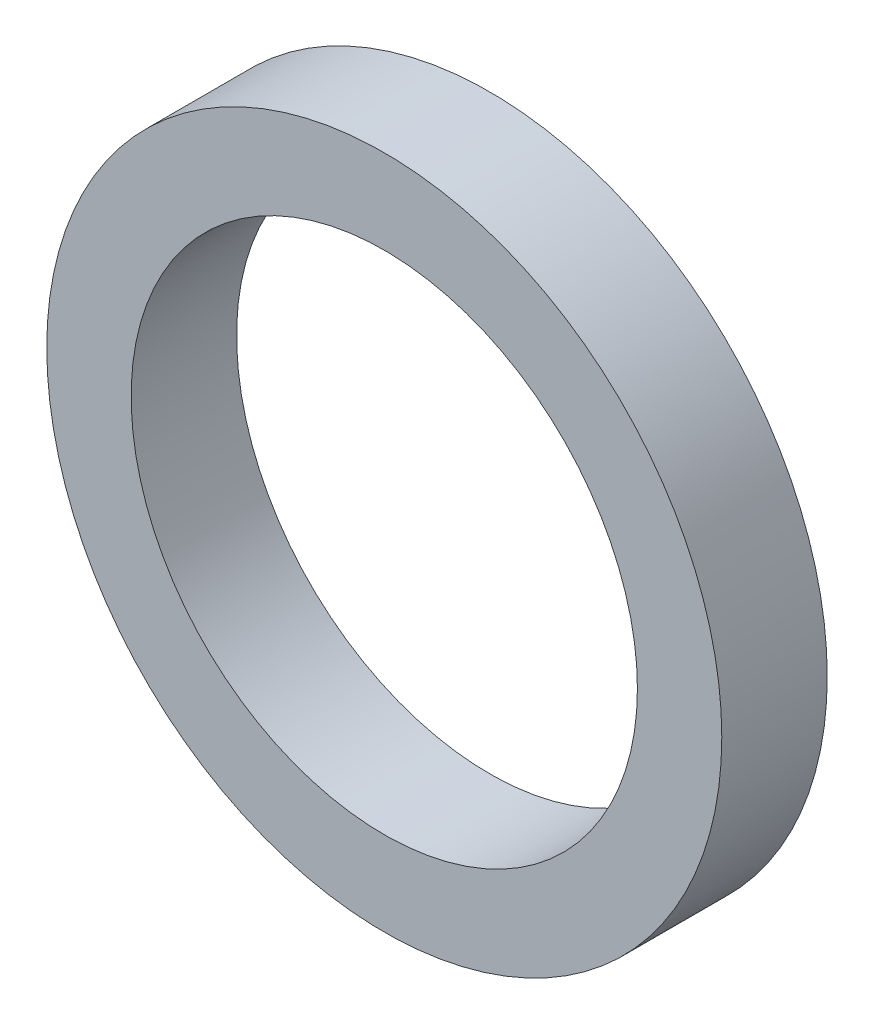
SolidWorks part; units mm, degrees
material "AISI 1020"
ref_plane "Front Plane" through (0, 0, 0) normal (0, 0, 1) x (1, 0, 0)
ref_plane "Top Plane" through (0, 0, 0) normal (0, 1, 0) x (1, 0, 0)
ref_plane "Right Plane" through (0, 0, 0) normal (1, 0, 0) x (0, 0, -1)
sketch "Sketch1" plane through (0, 0, 0) normal (0, 0, 1) x (1, 0, 0)
  circle A0 centre (0, 0) radius 12.7
  circle A1 centre (0, 0) radius 9.525
  dimension "D1" = 25.4
  dimension "D2" = 19.05
extrude "Boss-Extrude1" add sketch "Sketch1" along normal blind 3.9675
